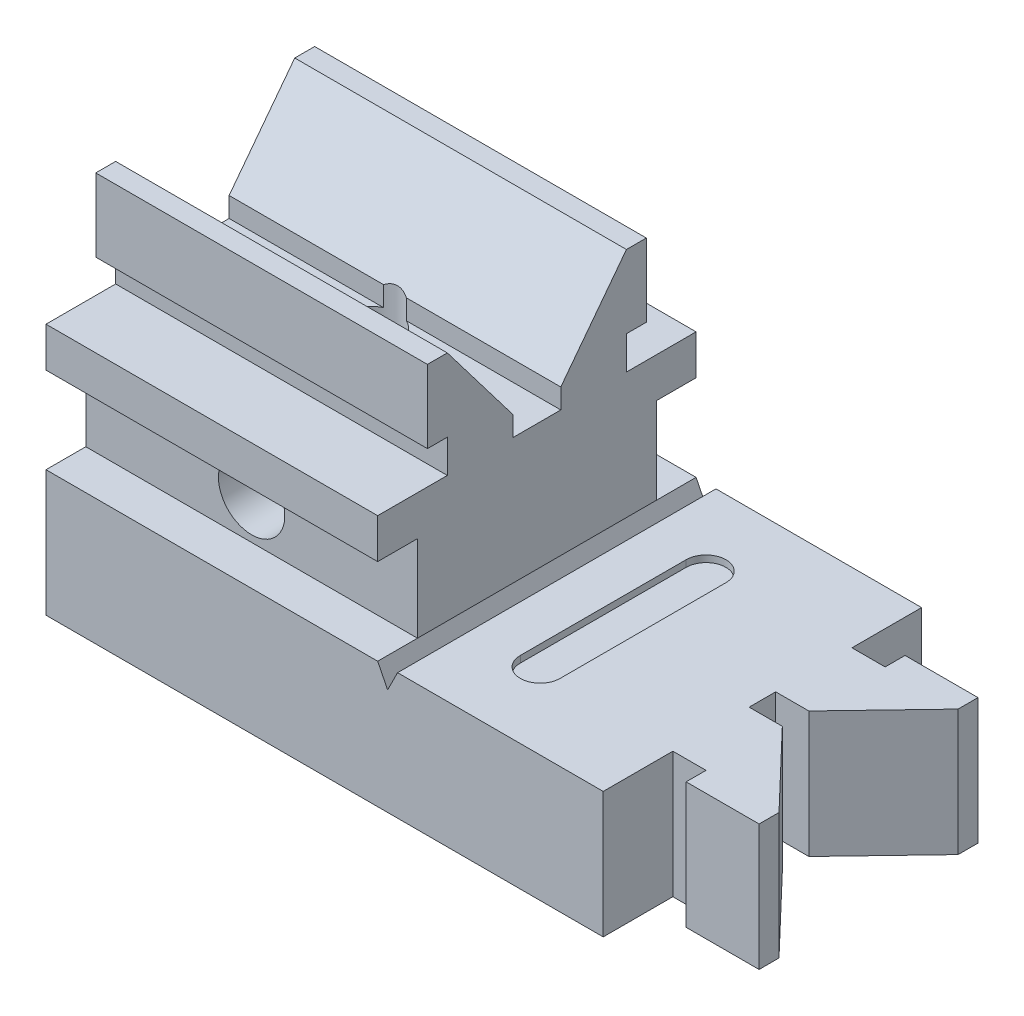
SolidWorks part; units mm, degrees
ref_plane "Front Plane" through (0, 0, 0) normal (0, 0, 1) x (1, 0, 0)
ref_plane "Top Plane" through (0, 0, 0) normal (0, 1, 0) x (1, 0, 0)
ref_plane "Right Plane" through (0, 0, 0) normal (1, 0, 0) x (0, 0, -1)
sketch "Sketch1" plane through (0, 0, 0) normal (0, 0, 1) x (1, 0, 0)
  line L0 (0, 0) -> (84, 0)
  line L1 (84, 0) -> (84, 19)
  line L2 (84, 19) -> (53, 19)
  line L6 (50, 19) -> (51.5, 16)
  line L7 (51.5, 16) -> (53, 19)
  line L8 (51.5, 16) -> (51.5, 9.6435) construction
  line L9 (0, 0) -> (0, 19)
  line L10 (0, 19) -> (50, 19)
  dimension "D1" = 84
  dimension "D2" = 19
  dimension "D3" = 3
  dimension "D4" = 3
  dimension "D5" = 50
extrude "Boss-Extrude2" add sketch "Sketch1" along normal mid plane 48
sketch "Sketch2" plane through (0, 0, 0) normal (0, 1, 0) x (1, 0, 0)
  line L0 (84, 2) -> (89, 2)
  line L1 (84, -24) -> (84, 24) construction
  line L2 (89, 2) -> (100, 13.5)
  line L3 (100, 13.5) -> (100, 16.5)
  line L4 (100, 16.5) -> (89, 16.5)
  line L5 (89, 16.5) -> (89, 13.5)
  line L6 (89, 13.5) -> (84, 13.5)
  line L7 (0, 0) -> (120.9781, 0) construction
  line L9 (84, 13.5) -> (84, 2)
  dimension "D1" = 2
  dimension "D2" = 5
  dimension "D3" = 13.5
  dimension "D4" = 16.5
  dimension "D5" = 11
extrude "Boss-Extrude3" add sketch "Sketch2" along normal blind 19
mirror "Mirror1" about plane through (0, 0, 0) normal (0, 0, 1) of "Boss-Extrude3"
sketch "Sketch3" plane through (0, 19, 0) normal (0, 1, 0) x (1, 0, 0)
  line L0 (63, 12.5) -> (63, -12.5) construction
  line L1 (66, 12.5) -> (66, -12.5)
  line L2 (60, 12.5) -> (60, -12.5)
  line L3 (0, 0) -> (33.0522, 0) construction
  line L4 (0, -24) -> (0, 24) construction
  arc A0 (66, 12.5) -> (60, 12.5) centre (63, 12.5) ccw
  arc A1 (60, -12.5) -> (66, -12.5) centre (63, -12.5) ccw
  point P2 (63, 0)
  point P10 (0, 0)
  point P11 (0, 0)
  dimension "D2" = 3
  dimension "D1" = 25
  dimension "D3" = 63
extrude "Cut-Extrude1" cut sketch "Sketch3" against normal blind 1
sketch "Sketch4" plane through (0, 0, 0) normal (1, 0, 0) x (0, 0, -1)
  line L0 (0, 0) -> (0, 41.4975) construction
  line L1 (-18, 19) -> (-18, 32)
  line L2 (-18, 32) -> (-24, 32)
  line L3 (-24, 32) -> (-24, 38)
  line L4 (-24, 38) -> (-13.5, 38)
  line L5 (-13.5, 38) -> (-13.5, 43)
  line L6 (-13.5, 43) -> (-16.5, 43)
  line L7 (-16.5, 43) -> (-16.5, 54)
  line L8 (-16.5, 54) -> (-13.5, 54)
  line L9 (-13.5, 54) -> (-3.6048, 41)
  line L10 (-3.6048, 41) -> (-3.6048, 38)
  line L11 (-3.6048, 38) -> (0, 38)
  line L12 (-24, 0) -> (-13.5, 0) construction
  line L13 (-24, 19) -> (-13.5, 19) construction
  line L14 (0, 38) -> (0, 19)
  line L15 (0, 19) -> (-18, 19)
  point P17 (-18.75, 0)
  dimension "D1" = 32
  dimension "D2" = 38
  dimension "D3" = 3
  dimension "D4" = 13.5
  dimension "D5" = 16.5
  dimension "D6" = 24
  dimension "D7" = 43
  dimension "D8" = 54
  dimension "D9" = 18
  dimension "D10" = 3.6048
extrude "Boss-Extrude4" add sketch "Sketch4" along normal blind 50
mirror "Mirror2" about plane through (0, 0, 0) normal (0, 0, 1) of "Boss-Extrude4"
sketch "Sketch5" plane through (0, 0, 0) normal (0, 1, 0) x (1, 0, 0)
  line L0 (50, -24) -> (0, -24) construction
  line L1 (0, -13.5) -> (0, -24) construction
  circle A0 centre (25, 0) radius 4
  dimension "D1" = 8
  dimension "D2" = 24
  dimension "D3" = 25
extrude "Cut-Extrude2" cut sketch "Sketch5" along normal through all
sketch "Sketch6" plane through (0, 0, 0) normal (0, 0, 1) x (1, 0, 0)
  line L0 (0, 0) -> (84, 0) construction
  line L1 (0, 19) -> (0, 0) construction
  circle A0 centre (25, 25) radius 5
  dimension "D1" = 10
  dimension "D2" = 25
  dimension "D3" = 25
extrude "Cut-Extrude3" cut sketch "Sketch6" against normal through all both and the other way through all
